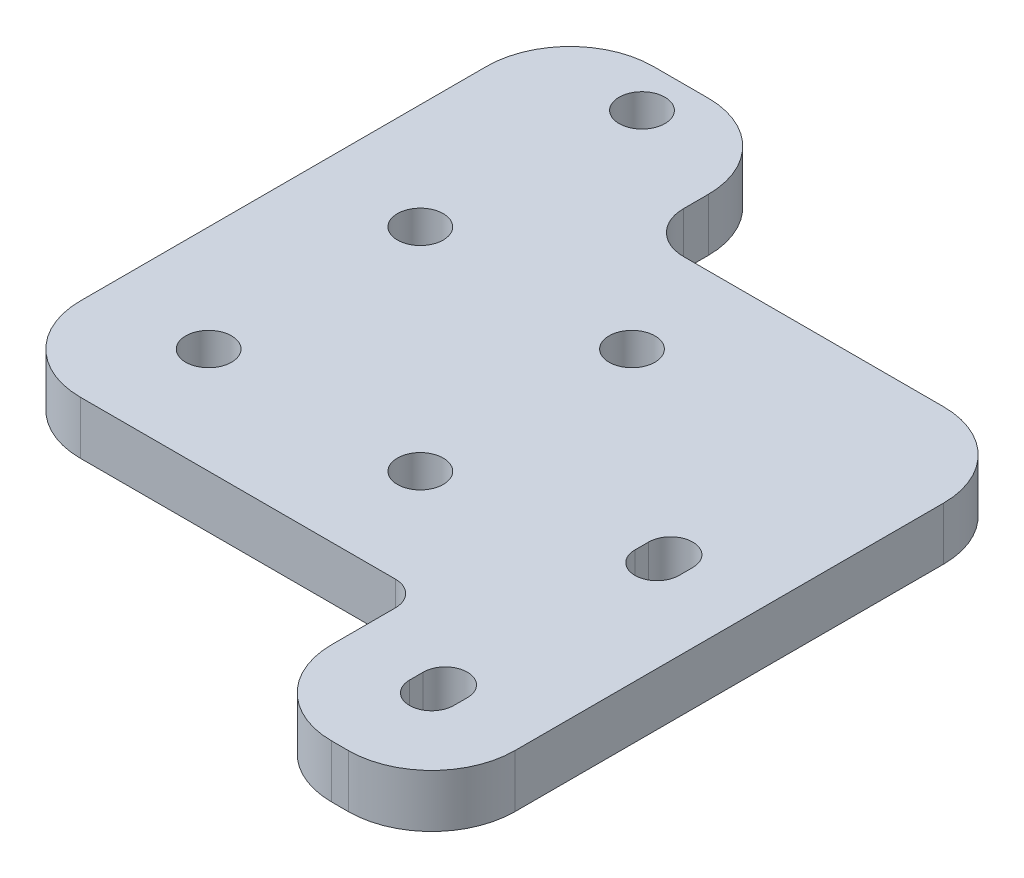
SolidWorks part; units mm, degrees
material "6061-T6 (SS)"
ref_plane "Front" through (0, 0, 0) normal (0, 0, 1) x (1, 0, 0)
ref_plane "Top" through (0, 0, 0) normal (0, 1, 0) x (1, 0, 0)
ref_plane "Right" through (0, 0, 0) normal (1, 0, 0) x (0, 0, -1)
sketch "Sketch1" plane through (0, 0, 0) normal (0, 1, 0) x (1, 0, 0)
  line L0 (0, 0) -> (47.4, 0) construction
  line L1 (25.4, -25.4) -> (-25.4, -25.4)
  line L2 (25.4, -25.4) -> (25.4, 25.4) construction
  line L3 (25.4, 25.4) -> (-25.4, 25.4) construction
  line L4 (-25.4, -25.4) -> (-25.4, 25.4)
  line L5 (25.4, -25.4) -> (-25.4, 25.4) construction
  line L6 (25.4, 25.4) -> (-25.4, -25.4) construction
  line L7 (1.2, 25.4) -> (1.2, 76.2) construction
  line L8 (-12.7, 25.4) -> (-12.7, -25.4) construction
  line L9 (12.7, -25.4) -> (12.7, 25.4) construction
  line L10 (0, 0) -> (-25.4, 0) construction
  line L11 (-12.7, 0) -> (-12.7, 25.4) construction
  line L12 (-12.7, 12.7) -> (12.7, 12.7) construction
  line L13 (5.5675, -41.4) -> (47.4, -41.4) construction
  line L14 (25.4, -25.4) -> (25.4, -46.04)
  line L15 (25.4, -46.04) -> (36.4, -46.04)
  line L17 (36.4, -33.4) -> (36.4, 25.4) construction
  line L18 (36.4, -8) -> (36.4, -6.36) construction
  line L26 (47.4, -41.4) -> (47.4, 0) construction
  line L30 (47.4, 0) -> (0, 0) construction
  line L31 (1.2, 76.2) -> (-49.6, 76.2) construction
  line L32 (36.4, -46.04) -> (47.4, -46.04)
  line L33 (47.4, -46.04) -> (47.4, 25.4)
  line L34 (47.4, 25.4) -> (25.4, 25.4)
  line L36 (36.4, -35.04) -> (36.4, -33.4) construction
  line L37 (36.4, -35.04) -> (36.4, -46.04) construction
  line L38 (-49.6, 76.2) -> (-49.6, 25.4) construction
  line L39 (-49.6, -25.4) -> (-25.4, -25.4) construction
  line L40 (-49.6, 25.4) -> (-25.4, 25.4) construction
  line L41 (-11.5, 25.4) -> (-11.5, 76.2) construction
  line L42 (-25.4, 25.4) -> (-25.4, 43.35)
  line L43 (-25.4, 43.35) -> (1.2, 43.35)
  line L44 (1.2, 43.35) -> (1.2, 25.4)
  line L45 (1.2, 25.4) -> (25.4, 25.4)
  circle A0 centre (-12.7, 12.7) radius 2.5 construction
  circle A1 centre (12.7, 12.7) radius 2.5 construction
  circle A2 centre (-12.7, -12.7) radius 2.5 construction
  circle A3 centre (12.7, -12.7) radius 2.5 construction
  circle A4 centre (36.4, -6.36) radius 6.36 construction
  circle A5 centre (36.4, -8) radius 8 construction
  circle A6 centre (-11.5, 38.1) radius 5.25 construction
  circle A10 centre (36.4, -35.04) radius 6.36 construction
  circle A11 centre (36.4, -35.04) radius 11 construction
  circle A15 centre (-11.5, 38.1) radius 2.5 construction
  circle A20 centre (36.4, -35.04) radius 2.5 construction
  circle A25 centre (36.4, -33.4) radius 8 construction
  circle A26 centre (36.4, -33.4) radius 11 construction
  point P0 (0, 0)
  dimension "D6" = 5
  dimension "D7" = 22
  dimension "D9" = 16
  dimension "D11" = 10.5
  dimension "D12" = 16
  dimension "D16" = 12.7
  dimension "D8" = 12.72
  dimension "D10" = 5
  dimension "D1" = 50.8
  dimension "D2" = 50.8
  dimension "D3" = 50.8
  dimension "D4" = 12.7
  dimension "D5" = 25.4
  dimension "D14" = 50.8
  dimension "D15" = 24.2
  dimension "D22" = 12.7
extrude "Boss-Extrude1" add sketch "Sketch1" along normal blind 6.35
hole_wizard "M5 Clearance Hole1" positions "Sketch3" profile "Sketch2" hole size "M5" standard "ISO" end condition through all
sketch "Sketch3" plane through (0, 6.35, 0) normal (0, 1, 0) x (1, 0, 0)
  point P0 (-12.7, 12.7)
  point P3 (12.7, 12.7)
  point P6 (12.7, -12.7)
  point P9 (-12.7, -12.7)
  point P15 (-11.5, 38.1)
sketch "Sketch2" plane through (-12.7, 6.35, -12.7) normal (1, 0, 0) x (0, 0, 1)
  line L0 (0, 0) -> (0, 6.35)
  line L1 (0, 6.35) -> (2.75, 6.35)
  line L2 (2.75, 6.35) -> (2.75, 0)
  line L5 (2.75, 0) -> (0, 0)
  line L11 (0, -6.35) -> (0, 107.95) construction
  dimension "Thru Hole Dia." = 5.5
  dimension "Thru Hole Depth" = 6.35
sketch "Sketch7" plane through (0, 6.35, 0) normal (0, 1, 0) x (1, 0, 0)
  line L0 (36.4, -6.36) -> (36.4, -8) construction
  line L1 (36.4, -33.4) -> (36.4, -35.04) construction
  line L2 (33.75, -33.4) -> (33.75, -35.04)
  line L3 (33.75, -6.36) -> (33.75, -8)
  line L4 (39.05, -33.4) -> (39.05, -35.04)
  line L5 (39.05, -6.36) -> (39.05, -8)
  arc A0 (33.75, -33.4) -> (39.05, -33.4) centre (36.4, -33.4) cw
  arc A1 (33.75, -35.04) -> (39.05, -35.04) centre (36.4, -35.04) ccw
  arc A2 (33.75, -6.36) -> (39.05, -6.36) centre (36.4, -6.36) cw
  arc A3 (33.75, -8) -> (39.05, -8) centre (36.4, -8) ccw
  dimension "D1" = 2.65
  dimension "D2" = 2.65
extrude "Cut-Extrude2" cut sketch "Sketch7" against normal through all
fillet "Fillet1" radius 10 6 edges at (47.4, 3.175, 46.04) (47.4, 3.175, -25.4) (-25.4, 3.175, 25.4) (-25.4, 3.175, -43.35) (1.2, 3.175, -43.35) (25.4, 3.175, 46.04)
fillet "Fillet2" radius 3 1 edges at (25.4, 3.175, 25.4)
fillet "Fillet3" radius 5 1 edges at (1.2, 3.175, -25.4)
